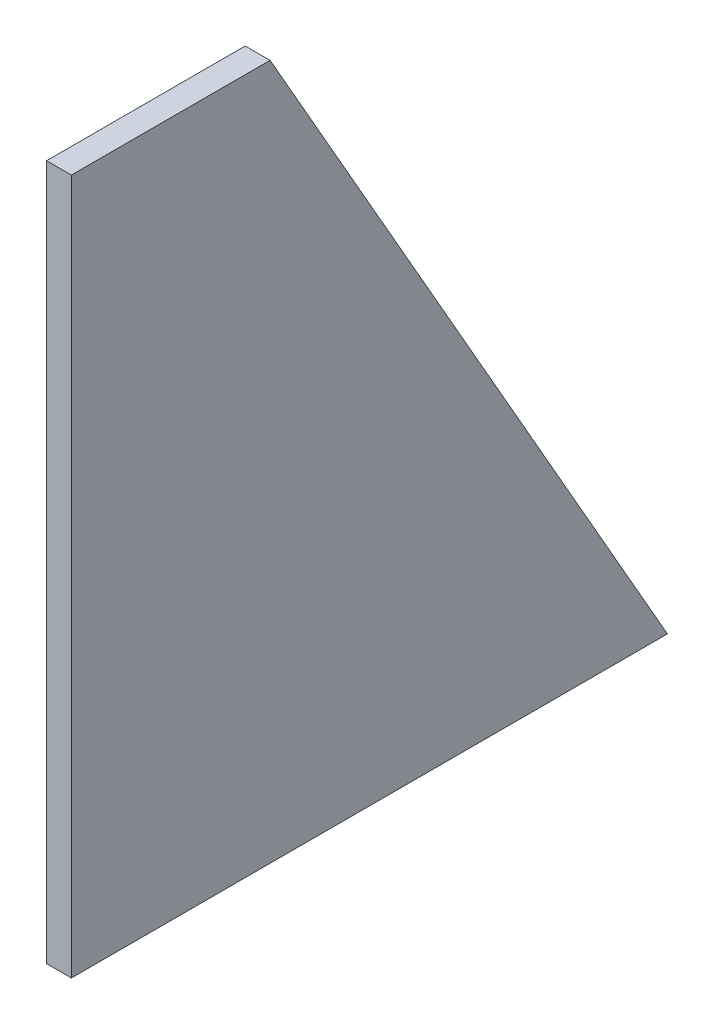
SolidWorks part; units mm, degrees
material "Custom Plastic"
ref_plane "Front Plane" through (0, 0, 0) normal (0, 0, 1) x (1, 0, 0)
ref_plane "Top Plane" through (0, 0, 0) normal (0, 1, 0) x (1, 0, 0)
ref_plane "Right Plane" through (0, 0, 0) normal (1, 0, 0) x (0, 0, -1)
sketch "Sketch1" plane through (0, 0, 0) normal (1, 0, 0) x (0, 0, -1)
  line L1 (0, 0) -> (152.4, 0)
  line L2 (0, 0) -> (0, 177.8)
  line L3 (0, 177.8) -> (50.8, 177.8)
  line L5 (50.8, 177.8) -> (152.4, 0)
extrude "Boss-Extrude1" add sketch "Sketch1" along normal blind 6.35 contours L2 L3 L5 L1
